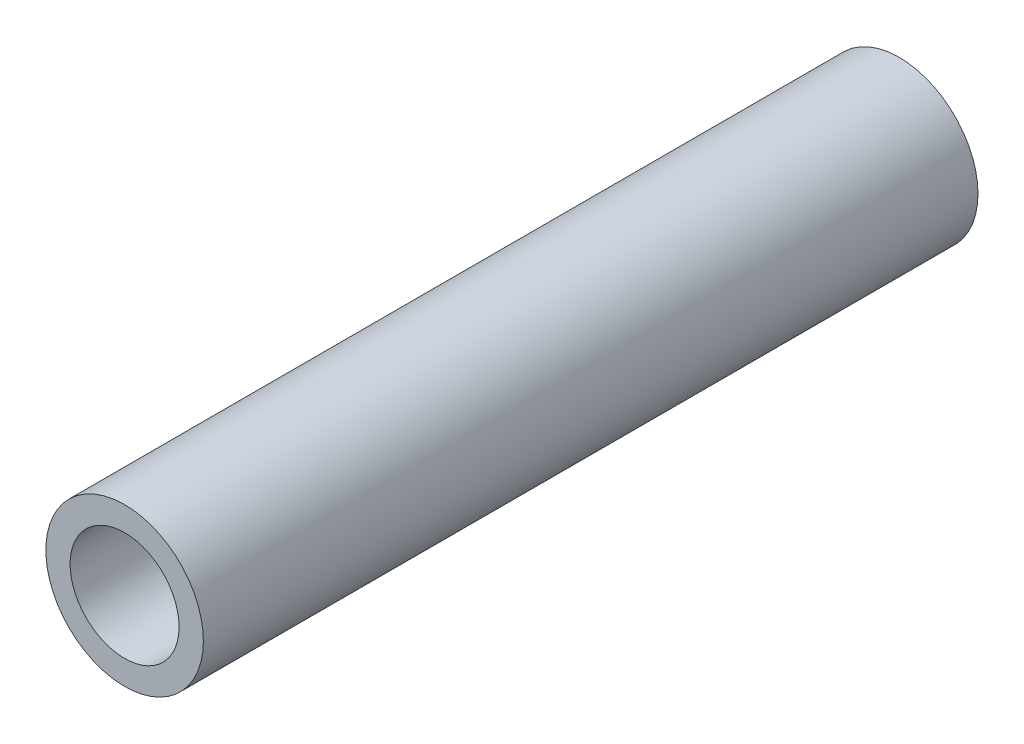
SolidWorks part; units mm, degrees
material "PVC Rigid"
ref_plane "Front Plane" through (0, 0, 0) normal (0, 0, 1) x (1, 0, 0)
ref_plane "Top Plane" through (0, 0, 0) normal (0, 1, 0) x (1, 0, 0)
ref_plane "Right Plane" through (0, 0, 0) normal (1, 0, 0) x (0, 0, -1)
sketch "Sketch1" plane through (0, 0, 0) normal (0, 0, 1) x (1, 0, 0)
  circle A0 centre (0, 0) radius 7.747
  circle A1 centre (0, 0) radius 5.3594
  dimension "D1" = 15.494
  dimension "D2" = 10.7188
extrude "Boss-Extrude1" add sketch "Sketch1" along normal blind 76.2
